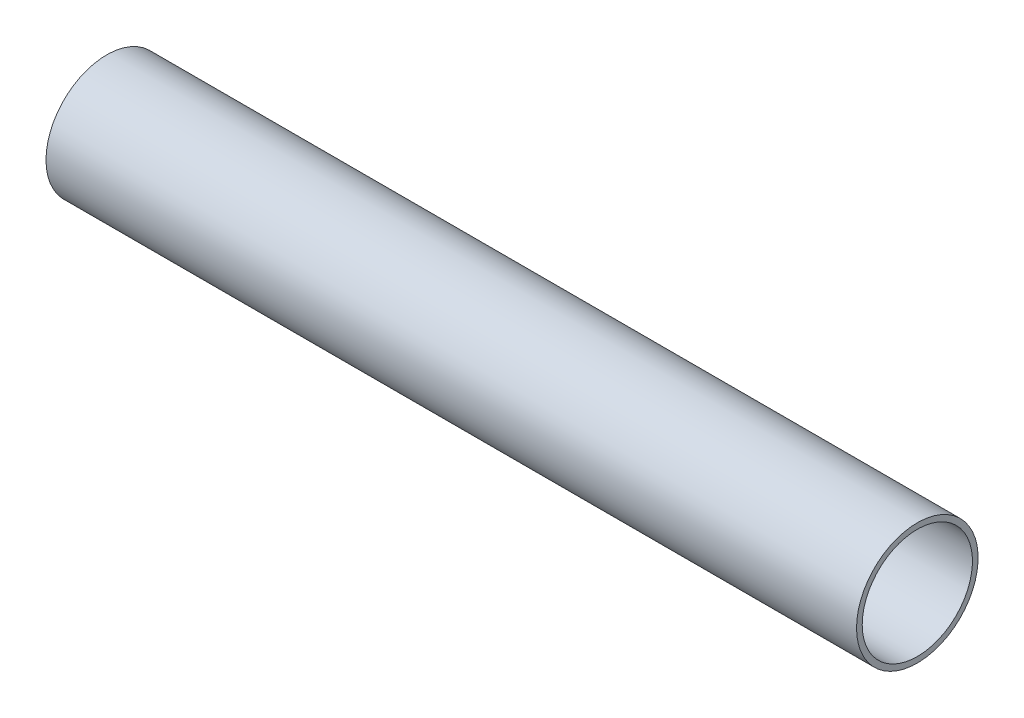
SolidWorks part; units mm, degrees
ref_plane "Front Plane" through (0, 0, 0) normal (0, 0, 1) x (1, 0, 0)
ref_plane "Top Plane" through (0, 0, 0) normal (0, 1, 0) x (1, 0, 0)
ref_plane "Right Plane" through (0, 0, 0) normal (1, 0, 0) x (0, 0, -1)
sketch "Sketch1" plane through (0, 0, 0) normal (0, 1, 0) x (1, 0, 0)
  line L0 (0, 0) -> (127, 0) construction
  line L1 (0, 9.525) -> (127, 9.525)
  line L2 (127, 9.525) -> (127, 8.636)
  line L3 (127, 8.636) -> (0, 8.636)
  line L4 (0, 8.636) -> (0, 9.525)
  dimension "D1" = 127
  dimension "D2" = 9.525
  dimension "D3" = 0.889
  dimension "D4" = 127
revolve "Revolve1" add sketch "Sketch1" angle 360 about L0
